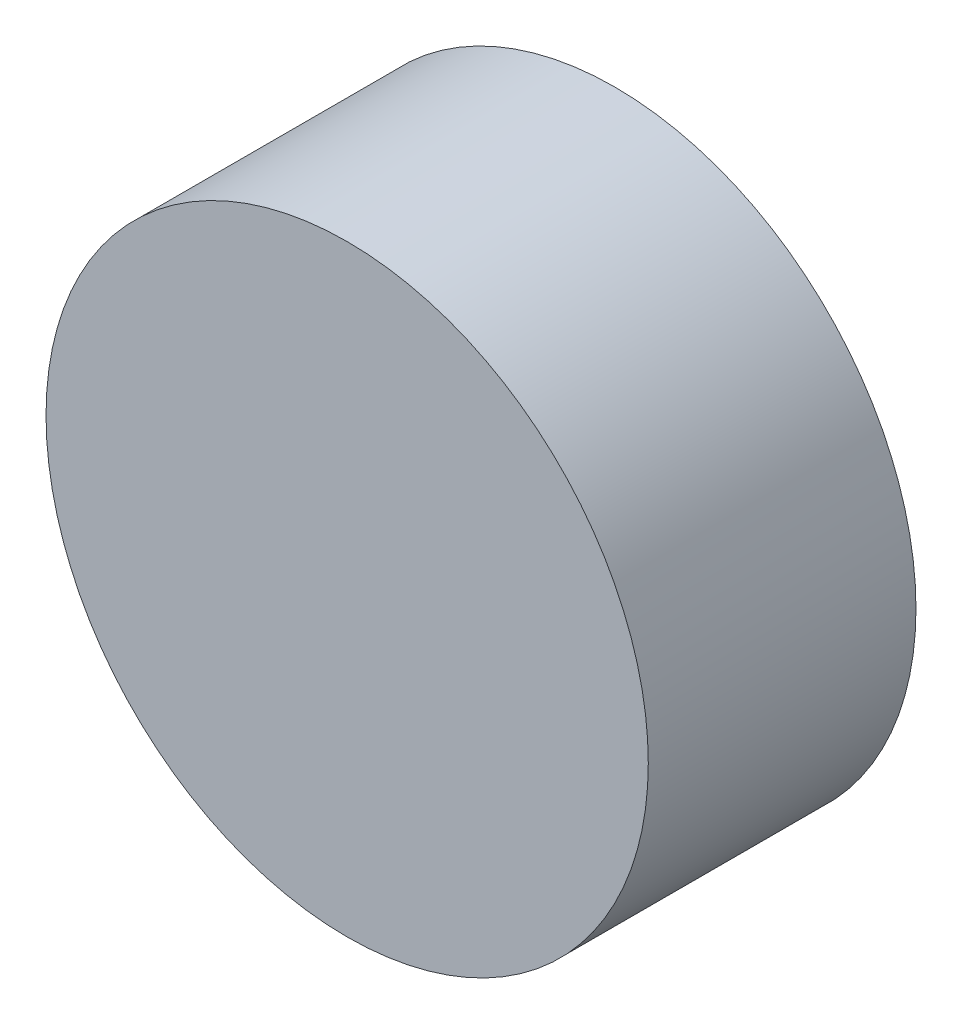
SolidWorks part; units mm, degrees
ref_plane "Front Plane" through (0, 0, 0) normal (0, 0, 1) x (1, 0, 0)
ref_plane "Top Plane" through (0, 0, 0) normal (0, 1, 0) x (1, 0, 0)
ref_plane "Right Plane" through (0, 0, 0) normal (1, 0, 0) x (0, 0, -1)
sketch "Sketch1" plane through (0, 0, 0) normal (0, 0, 1) x (1, 0, 0)
  circle A0 centre (0, 0) radius 22.5
  dimension "D1" = 45
extrude "Boss-Extrude1" add sketch "Sketch1" along normal blind 20
